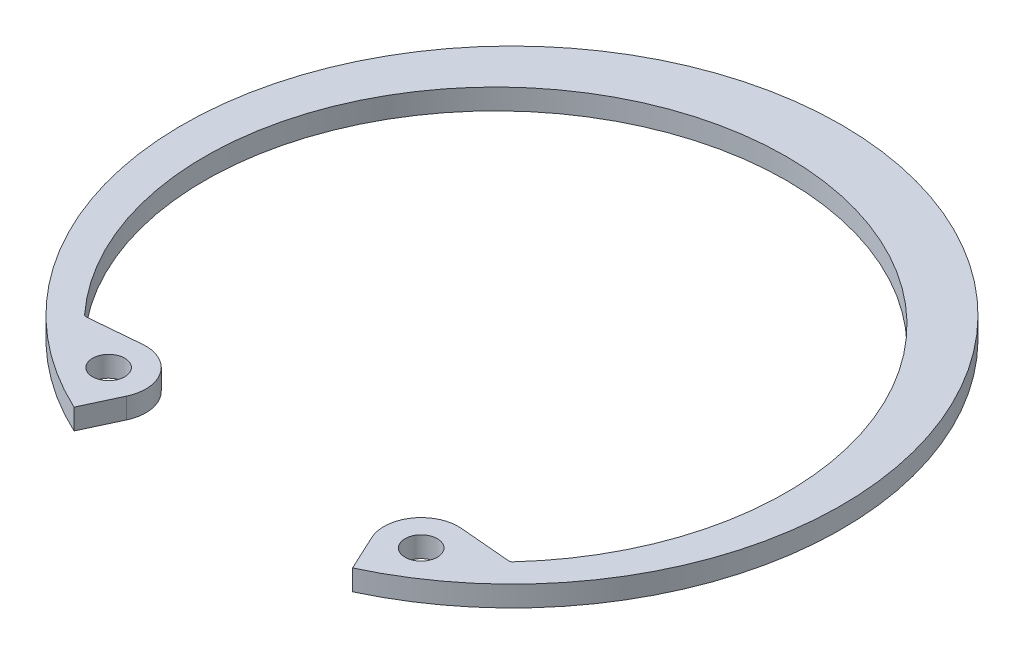
SolidWorks part; units mm, degrees
material "Cast Carbon Steel"
ref_plane "Front" through (0, 0, 0) normal (0, 0, 1) x (1, 0, 0)
ref_plane "Top" through (0, 0, 0) normal (0, 1, 0) x (1, 0, 0)
ref_plane "Right" through (0, 0, 0) normal (1, 0, 0) x (0, 0, -1)
sketch "Sketch2" plane through (0, 0, 0) normal (0, 1, 0) x (1, 0, 0)
  line L0 (0, 0) -> (0, -20.2438) construction
  line L1 (-13.0721, -13.1859) -> (-14.2524, -14.3764) construction
  line L2 (8.5554, -18.3471) -> (7.5276, -16.1429)
  line L3 (-8.5554, -18.3471) -> (-7.5276, -16.1429)
  line L4 (0, 16.8656) -> (0, 20.2438) construction
  line L5 (13.0721, -13.1859) -> (9.7986, -12.8995)
  line L6 (-13.0721, -13.1859) -> (-9.7986, -12.8995)
  line L7 (8.3774, -13.2448) -> (-0.5081, -18.8649) construction
  line L8 (-0.5081, -18.8649) -> (1.9358, -22.7289) construction
  line L9 (1.9358, -22.7289) -> (10.8214, -17.1088) construction
  line L10 (8.3774, -13.2448) -> (10.8214, -17.1088) construction
  line L11 (9.5994, -15.1768) -> (7.5276, -16.1429) construction
  line L12 (9.5994, -15.1768) -> (10.8214, -17.1088) construction
  line L13 (8.3774, -13.2448) -> (-8.3774, -13.2448) construction
  line L14 (-8.3774, -13.2448) -> (-10.8214, -17.1088) construction
  line L15 (-20.2438, 0) -> (20.2438, 0) construction
  arc A1 (8.5554, -18.3471) -> (-8.5554, -18.3471) centre (0, 0) ccw
  arc A2 (13.0721, -13.1859) -> (-13.0721, -13.1859) centre (0, -1.0033) ccw
  circle A3 centre (0, 0) radius 20.2438 construction
  arc A4 (7.5276, -16.1429) -> (9.7986, -12.8995) centre (9.5994, -15.1768) cw
  arc A5 (-7.5276, -16.1429) -> (-9.7986, -12.8995) centre (-9.5994, -15.1768) ccw
  circle A6 centre (9.5994, -15.1768) radius 0.9906
  circle A7 centre (-9.5994, -15.1768) radius 0.9906
  arc A8 (13.0721, -13.1859) -> (-13.0721, -13.1859) centre (0, -1.0033) cw construction
  circle A9 centre (0, 0) radius 14.7955 construction
  point P5 (9.5994, -15.1768)
  point P10 (8.3774, -13.2448)
  dimension "D1" = 60
  dimension "D2" = 60
  dimension "L" = 29.591
  dimension "R" = 1.9812
  dimension "Df" = 40.4876
  dimension "H" = 4.572
  dimension "Angle" = 25
  dimension "Sec. Max" = 3.3782
  dimension "Sec. Min" = 1.6764
extrude "Extrude1" add sketch "Sketch2" against normal blind 1.27
fillet "Fillet1" radius 0.254 2 edges at (-13.0721, -0.635, 13.1859) (13.0721, -0.635, 13.1859)
sketch "Sketch3" plane through (0, 0, 0) normal (1, 0, 0) x (0, 0, -1)
  line L0 (-19.05, -13.2588) -> (-19.05, -1.3462)
  line L1 (-19.05, -1.3462) -> (-20.2438, -1.3462)
  line L2 (-20.2438, -1.3462) -> (-20.2438, 0.0762)
  line L3 (-20.2438, 0.0762) -> (-19.05, 0.0762)
  line L4 (-19.05, 0.0762) -> (-19.05, 1.9812)
  line L5 (-19.05, -13.2588) -> (-21.4376, -13.2588)
  line L6 (-19.05, -1.3462) -> (0, -1.3462) construction
  line L7 (-19.05, 1.9812) -> (-21.4376, 1.9812)
  line L8 (0, 130.3401) -> (0, 164.6301) construction
  line L9 (0, -1.3462) -> (0, 0.0762) construction
  line L10 (0, 0.0762) -> (-19.05, 0.0762) construction
  line L11 (-20.2438, -0.635) -> (0, -0.635) construction
  line L12 (0, -135.0899) -> (0, 130.3401) construction
  line L13 (-13.0939, -1.27) -> (16.8656, -1.27) construction
  line L14 (-21.4376, -13.2588) -> (-21.4376, 1.9812)
  dimension "D1" = 0.635
  dimension "Shaft Lg" = 15.24
  dimension "Dg" = 40.4876
  dimension "Db" = 38.1
  dimension "W" = 1.4224
  dimension "D2" = 1.1938
  dimension "D3" = 1.905
  dimension "D4" = 1.1938
revolve "Revolve1" [suppressed] add sketch "Sketch3" angle 360 about L8
delete or keep bodies "Body-Delete1" [suppressed] type delete bodies bodies 116
equation "\"D3@Sketch3\" = \"Shaft Lg@Sketch3\"/8"
equation "\"Shaft Lg@Sketch3\" = \"D1@Extrude1\"*12"
equation "\"D1@Sketch3\" = \"D1@Extrude1\"/2"
equation "\"D2@Sketch3\" = \"D4@Sketch3\""
